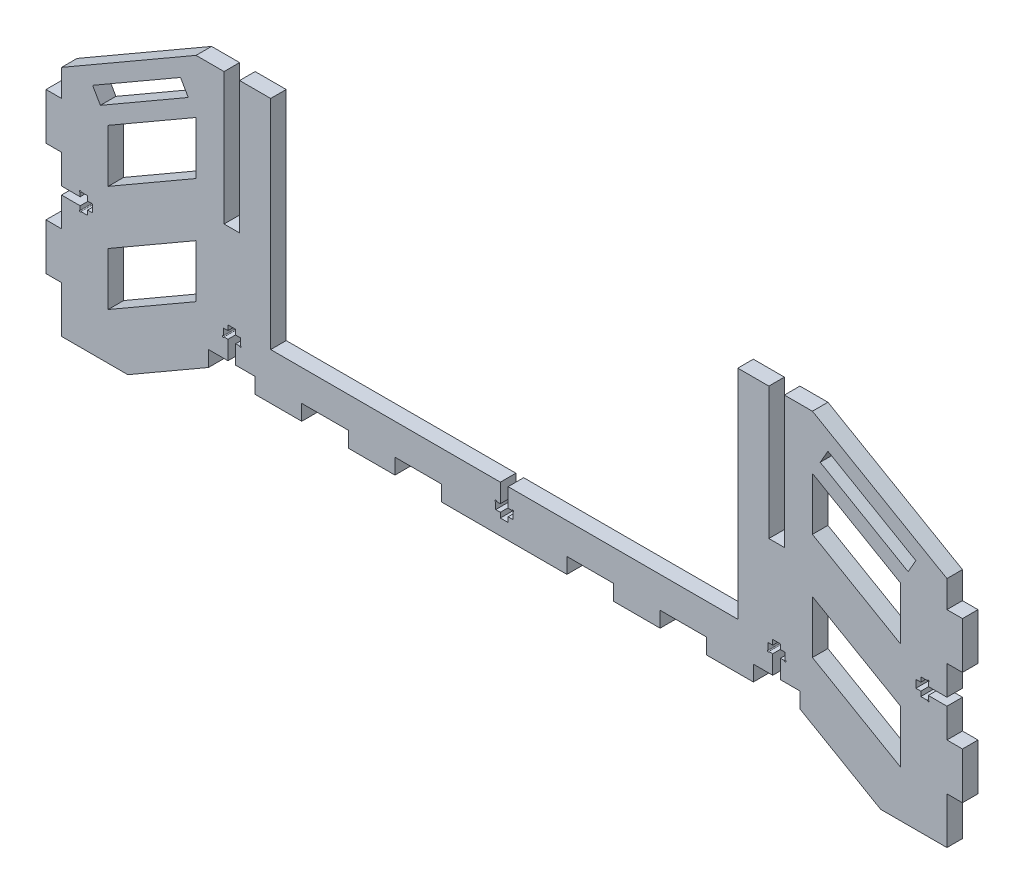
SolidWorks part; units mm, degrees
material "PMMA"
ref_plane "Front Plane" through (0, 0, 0) normal (0, 0, 1) x (1, 0, 0)
ref_plane "Top Plane" through (0, 0, 0) normal (0, 1, 0) x (1, 0, 0)
ref_plane "Right Plane" through (0, 0, 0) normal (1, 0, 0) x (0, 0, -1)
sketch "Schizzo1" plane through (0, 0, 0) normal (0, 0, 1) x (1, 0, 0)
  line L0 (-142.5, 75) -> (-142.5, 66.3397)
  line L1 (-142.5, 0) -> (142.5, 0)
  line L2 (142.5, 75) -> (142.5, 66.3397)
  line L3 (142.5, 75) -> (99.1987, 100)
  line L4 (99.1987, 100) -> (-99.1987, 100)
  line L5 (-99.1987, 100) -> (-142.5, 75)
  line L6 (95.1795, 85) -> (-95.1795, 85) construction
  line L7 (-95.1795, 85) -> (-127.5, 66.3397) construction
  line L8 (-127.5, 66.3397) -> (-127.5, 15) construction
  line L9 (-127.5, 15) -> (127.5, 15) construction
  line L10 (127.5, 15) -> (127.5, 66.3397) construction
  line L11 (127.5, 66.3397) -> (95.1795, 85) construction
  line L12 (-95.1795, 85) -> (-95.1795, 15) construction
  line L13 (95.1795, 85) -> (95.1795, 15) construction
  line L14 (-127.5, 66.3397) -> (127.5, 66.3397) construction
  line L15 (-142.5, 66.3397) -> (-147.5, 66.3397)
  line L16 (-147.5, 66.3397) -> (-147.5, 51.3397)
  line L17 (-147.5, 51.3397) -> (-142.5, 51.3397)
  line L18 (-142.5, 51.3397) -> (-142.5, 30)
  line L19 (-142.5, 30) -> (-147.5, 30)
  line L20 (-147.5, 30) -> (-147.5, 15)
  line L21 (-147.5, 15) -> (-142.5, 15)
  line L22 (-142.5, 15) -> (-142.5, 0)
  line L23 (-142.5, 75) -> (-142.5, 0) construction
  line L24 (142.5, 66.3397) -> (147.5, 66.3397)
  line L25 (142.5, 0) -> (142.5, 75) construction
  line L26 (147.5, 66.3397) -> (147.5, 51.3397)
  line L27 (147.5, 51.3397) -> (142.5, 51.3397)
  line L28 (142.5, 51.3397) -> (142.5, 30)
  line L29 (142.5, 30) -> (147.5, 30)
  line L30 (147.5, 30) -> (147.5, 15)
  line L31 (147.5, 15) -> (142.5, 15)
  line L32 (142.5, 15) -> (142.5, 0)
  point P2 (0, 0)
  dimension "D1" = 5
  dimension "D2" = 285
  dimension "D3" = 100
  dimension "D4" = 75
  dimension "D5" = 198.3975
  dimension "D7" = 190.359
  dimension "D8" = 15
  dimension "D9" = 150
  dimension "D10" = 21.3397
  dimension "D6" = 15
extrude "Estrusione-Estrusione1" add sketch "Schizzo1" along normal blind 5
sketch "Schizzo2" plane through (0, 0, 0) normal (0, 0, 1) x (1, 0, 0)
  line L0 (-99.1987, 82.6795) -> (-127.5, 66.3397)
  line L1 (-113.3494, 74.5096) -> (-120.8494, 87.5) construction
  line L2 (0, 0) -> (0, 100) construction
  line L3 (99.1987, 100) -> (-99.1987, 100) construction
  line L4 (-127.5, 49.3301) -> (-127.5, 66.3397)
  line L5 (99.1987, 31.3397) -> (99.1987, 48.3494)
  line L6 (-99.1987, 100) -> (-99.1987, 0) construction
  line L7 (99.1987, 31.3397) -> (127.5, 15)
  line L8 (127.5, 32.0096) -> (127.5, 15)
  line L9 (-95.1795, 15) -> (-121.1603, 0)
  line L10 (99.1987, 48.3494) -> (127.5, 32.0096)
  line L11 (-121.1603, 0) -> (121.1603, 0)
  line L12 (121.1603, 0) -> (95.1795, 15)
  line L13 (95.1795, 15) -> (-95.1795, 15)
  line L14 (-142.5, 0) -> (142.5, 0) construction
  line L15 (-99.1987, 31.3397) -> (-127.5, 15)
  line L16 (-99.1987, 65.6699) -> (-99.1987, 82.6795)
  line L17 (99.1987, 65.6699) -> (99.1987, 82.6795)
  line L18 (127.5, 49.3301) -> (99.1987, 65.6699)
  line L19 (127.5, 49.3301) -> (127.5, 66.3397)
  line L20 (-127.5, 49.3301) -> (-99.1987, 65.6699)
  line L21 (-99.1987, 48.3494) -> (-127.5, 32.0096)
  line L22 (-127.5, 32.0096) -> (-127.5, 15)
  line L23 (-99.1987, 31.3397) -> (-99.1987, 48.3494)
  line L24 (99.1987, 82.6795) -> (127.5, 66.3397)
  line L25 (-99.1987, 100) -> (-142.5, 75) construction
  line L26 (-127.5, 66.3397) -> (-135, 79.3301) construction
  line L27 (-132.5, 75) -> (-104.1987, 91.3397)
  line L28 (-132.5, 75) -> (-130, 70.6699)
  line L29 (-130, 70.6699) -> (-101.6987, 87.0096)
  line L30 (-104.1987, 91.3397) -> (-101.6987, 87.0096)
  line L31 (132.5, 75) -> (130, 70.6699)
  line L32 (132.5, 75) -> (104.1987, 91.3397)
  line L33 (104.1987, 91.3397) -> (101.6987, 87.0096)
  line L34 (130, 70.6699) -> (101.6987, 87.0096)
  point P42 (-131.25, 72.8349)
  point P44 (-131.25, 72.8349)
  point P46 (-115.8494, 78.8397)
  point P47 (-118.3494, 83.1699)
  dimension "D1" = 15
  dimension "D3" = 5
extrude "Taglio-Estrusione2" cut sketch "Schizzo2" along direction (0, 0, 1) on the side of the normal through all
sketch "Schizzo5" plane through (0, 0, 0) normal (0, 0, 1) x (1, 0, 0)
  line L0 (-95.1795, 15) -> (-95.1795, 20)
  line L1 (-95.1795, 20) -> (-80.1795, 20)
  line L2 (-80.1795, 20) -> (-80.1795, 15)
  line L3 (-80.1795, 15) -> (-95.1795, 15)
  line L4 (-65.1795, 20) -> (-65.1795, 15)
  line L5 (-65.1795, 15) -> (-50.1795, 15)
  line L6 (-50.1795, 15) -> (-50.1795, 20)
  line L7 (-50.1795, 20) -> (-65.1795, 20)
  line L8 (-35.1795, 15) -> (-35.1795, 20)
  line L9 (-35.1795, 20) -> (-20.1795, 20)
  line L10 (-20.1795, 20) -> (-20.1795, 15)
  line L11 (-20.1795, 15) -> (-35.1795, 15)
  line L12 (-127.5, 15) -> (127.5, 15) construction
  line L13 (-95.1795, 85) -> (-95.1795, 15) construction
  line L14 (0, 15) -> (0, 100) construction
  line L15 (35.1795, 15) -> (35.1795, 20)
  line L16 (20.1795, 15) -> (35.1795, 15)
  line L17 (20.1795, 20) -> (20.1795, 15)
  line L18 (35.1795, 20) -> (20.1795, 20)
  line L19 (50.1795, 15) -> (50.1795, 20)
  line L20 (65.1795, 15) -> (50.1795, 15)
  line L21 (65.1795, 20) -> (65.1795, 15)
  line L22 (50.1795, 20) -> (65.1795, 20)
  line L23 (95.1795, 15) -> (95.1795, 20)
  line L24 (80.1795, 15) -> (95.1795, 15)
  line L25 (80.1795, 20) -> (80.1795, 15)
  line L26 (95.1795, 20) -> (80.1795, 20)
  line L27 (-95.1795, 57.5) -> (95.1795, 57.5) construction
  line L28 (-95.1795, 15) -> (-121.1603, 0) construction
  line L29 (95.1795, 85) -> (95.1795, 15) construction
  line L30 (99.1987, 100) -> (-99.1987, 100) construction
  line L31 (90.1795, 100) -> (85.1795, 100)
  line L32 (-90.1795, 100) -> (-85.1795, 100)
  line L33 (-90.1795, 100) -> (-90.1795, 57.5)
  line L34 (-90.1795, 57.5) -> (-85.1795, 57.5)
  line L35 (-85.1795, 100) -> (-85.1795, 57.5)
  line L36 (90.1795, 100) -> (90.1795, 57.5)
  line L37 (90.1795, 57.5) -> (85.1795, 57.5)
  line L38 (85.1795, 100) -> (85.1795, 57.5)
  line L40 (-75.1795, 100) -> (75.1795, 100)
  line L41 (-75.1795, 100) -> (-75.1795, 30)
  line L42 (-75.1795, 30) -> (75.1795, 30)
  line L43 (75.1795, 100) -> (75.1795, 30)
  dimension "D1" = 5
  dimension "D2" = 15
  dimension "D3" = 15
  dimension "D4" = 15
  dimension "D5" = 42.5
  dimension "D6" = 42.5
  dimension "D7" = 5
  dimension "D8" = 5
  dimension "D9" = 10
  dimension "D10" = 10
  dimension "D11" = 15
  dimension "D12" = 190.359
  dimension "D13" = 40.359
extrude "Taglio-Estrusione3" cut sketch "Schizzo5" along direction (0, 0, 1) on the side of the normal through all
sketch "Schizzo6" plane through (0, 0, 0) normal (0, 0, 1) x (1, 0, 0)
  line L0 (-142.5, 51.3397) -> (-142.5, 30) construction
  line L1 (-142.5, 40.6699) -> (-120, 40.6699) construction
  line L2 (-142.5, 41.9199) -> (-136.5, 41.9199)
  line L3 (-136.5, 41.9199) -> (-136.5, 43.4199)
  line L4 (-136.5, 43.4199) -> (-134.1, 43.4199)
  line L5 (-134.1, 43.4199) -> (-134.1, 41.9199)
  line L6 (-134.1, 41.9199) -> (-132.5, 41.9199)
  line L7 (-132.5, 41.9199) -> (-132.5, 39.4199)
  line L8 (-132.5, 39.4199) -> (-134.1, 39.4199)
  line L9 (-134.1, 39.4199) -> (-134.1, 37.9199)
  line L10 (-134.1, 37.9199) -> (-136.5, 37.9199)
  line L11 (-136.5, 37.9199) -> (-136.5, 39.4199)
  line L12 (-136.5, 39.4199) -> (-142.5, 39.4199)
  line L13 (-142.5, 39.4199) -> (-142.5, 41.9199)
  line L14 (0, 0) -> (0, 100) construction
  line L15 (134.1, 43.4199) -> (134.1, 41.9199)
  line L16 (136.5, 43.4199) -> (134.1, 43.4199)
  line L17 (136.5, 41.9199) -> (136.5, 43.4199)
  line L18 (142.5, 41.9199) -> (136.5, 41.9199)
  line L19 (142.5, 39.4199) -> (142.5, 41.9199)
  line L20 (136.5, 39.4199) -> (142.5, 39.4199)
  line L21 (136.5, 37.9199) -> (136.5, 39.4199)
  line L22 (134.1, 37.9199) -> (136.5, 37.9199)
  line L23 (134.1, 39.4199) -> (134.1, 37.9199)
  line L24 (132.5, 39.4199) -> (134.1, 39.4199)
  line L25 (132.5, 41.9199) -> (132.5, 39.4199)
  line L26 (134.1, 41.9199) -> (132.5, 41.9199)
  line L27 (-90.1795, 57.5) -> (-85.1795, 57.5) construction
  line L28 (-87.6795, 57.5) -> (-87.6795, 2.5) construction
  line L29 (-80.1795, 20) -> (-95.1795, 20) construction
  line L30 (85.1795, 57.5) -> (90.1795, 57.5) construction
  line L31 (87.6795, 57.5) -> (87.6795, 20) construction
  line L32 (95.1795, 20) -> (80.1795, 20) construction
  line L33 (-87.6795, 20) -> (-87.6795, 30) construction
  line L34 (-88.9295, 20) -> (-88.9295, 26)
  line L35 (-88.9295, 26) -> (-90.4295, 26)
  line L36 (-90.4295, 26) -> (-90.4295, 28.4)
  line L37 (-90.4295, 28.4) -> (-88.9295, 28.4)
  line L38 (-88.9295, 28.4) -> (-88.9295, 30)
  line L39 (-88.9295, 30) -> (-86.4295, 30)
  line L40 (-86.4295, 30) -> (-86.4295, 28.4)
  line L41 (-86.4295, 28.4) -> (-84.9295, 28.4)
  line L42 (-84.9295, 28.4) -> (-84.9295, 26)
  line L43 (-84.9295, 26) -> (-86.4295, 26)
  line L44 (-86.4295, 26) -> (-86.4295, 20)
  line L45 (-86.4295, 20) -> (-88.9295, 20)
  line L46 (86.4295, 20) -> (88.9295, 20)
  line L47 (86.4295, 26) -> (86.4295, 20)
  line L48 (84.9295, 26) -> (86.4295, 26)
  line L49 (84.9295, 28.4) -> (84.9295, 26)
  line L50 (86.4295, 28.4) -> (84.9295, 28.4)
  line L51 (86.4295, 30) -> (86.4295, 28.4)
  line L52 (88.9295, 30) -> (86.4295, 30)
  line L53 (88.9295, 28.4) -> (88.9295, 30)
  line L54 (90.4295, 28.4) -> (88.9295, 28.4)
  line L55 (90.4295, 26) -> (90.4295, 28.4)
  line L56 (88.9295, 26) -> (90.4295, 26)
  line L57 (88.9295, 20) -> (88.9295, 26)
  line L58 (0, 32.4779) -> (0, 27.5221) construction
  line L59 (0, 20) -> (0, 30) construction
  line L60 (-1.25, 20) -> (-1.25, 21.6)
  line L61 (-1.25, 21.6) -> (-2.75, 21.6)
  line L62 (-2.75, 21.6) -> (-2.75, 24)
  line L63 (-2.75, 24) -> (-1.25, 24)
  line L64 (-1.25, 24) -> (-1.25, 30)
  line L65 (-1.25, 30) -> (1.25, 30)
  line L66 (1.25, 30) -> (1.25, 24)
  line L67 (1.25, 24) -> (2.75, 24)
  line L68 (2.75, 24) -> (2.75, 21.6)
  line L69 (2.75, 21.6) -> (1.25, 21.6)
  line L70 (1.25, 21.6) -> (1.25, 20)
  line L71 (1.25, 20) -> (-1.25, 20)
  line L73 (-75.1795, 30) -> (75.1795, 30) construction
  dimension "D1" = 5.5
  dimension "D2" = 2.5
  dimension "D3" = 1.25
  dimension "D4" = 2.75
  dimension "D5" = 2.4
  dimension "D6" = 10
  dimension "D7" = 5.5
  dimension "D8" = 2.5
  dimension "D9" = 1.25
  dimension "D10" = 2.75
  dimension "D11" = 2.4
  dimension "D12" = 10
  dimension "D13" = 90
  dimension "D14" = 90
  dimension "D15" = 5.5
  dimension "D16" = 2.5
  dimension "D17" = 1.25
  dimension "D18" = 2.75
  dimension "D19" = 2.4
  dimension "D20" = 10
  dimension "D21" = 90
  dimension "D22" = 90
  dimension "D23" = 6
  dimension "D24" = 6
  dimension "D25" = 6
extrude "Taglio-Estrusione4" cut sketch "Schizzo6" along direction (0, 0, 1) on the side of the normal through all
sketch "Schizzo7" plane through (0, 0, 5) normal (0, 0, 1) x (1, 0, 0)
  circle A0 centre (-136.5, 43.4199) radius 0.25
  circle A1 centre (-136.5, 37.9199) radius 0.25
  circle A2 centre (-90.4295, 26) radius 0.25
  circle A3 centre (-84.9295, 26) radius 0.25
  circle A4 centre (-2.75, 24) radius 0.25
  circle A5 centre (2.75, 24) radius 0.25
  circle A6 centre (84.9295, 26) radius 0.25
  circle A7 centre (90.4295, 26) radius 0.25
  circle A8 centre (136.5, 43.4199) radius 0.25
  circle A9 centre (136.5, 37.9199) radius 0.25
  dimension "D1" = 0.5
  dimension "D2" = 0.5
  dimension "D3" = 0.5
  dimension "D4" = 0.5
  dimension "D5" = 0.5
extrude "Taglio-Estrusione5" cut sketch "Schizzo7" against normal blind 10
equation "\"Thickness\"=5"
equation "\"D1@Estrusione-Estrusione1\"=\"Thickness\""
equation "\"D1@Schizzo5\"=\"Thickness\""
equation "\"D7@Schizzo5\"=\"Thickness\""
equation "\"D9@Schizzo5\"=2*\"Thickness\""
equation "\"D10@Schizzo5\"=2*\"Thickness\""
equation "\"D1@Schizzo1\"=\"Thickness\""
equation "\"D3@Schizzo2\"=\"Thickness\""
